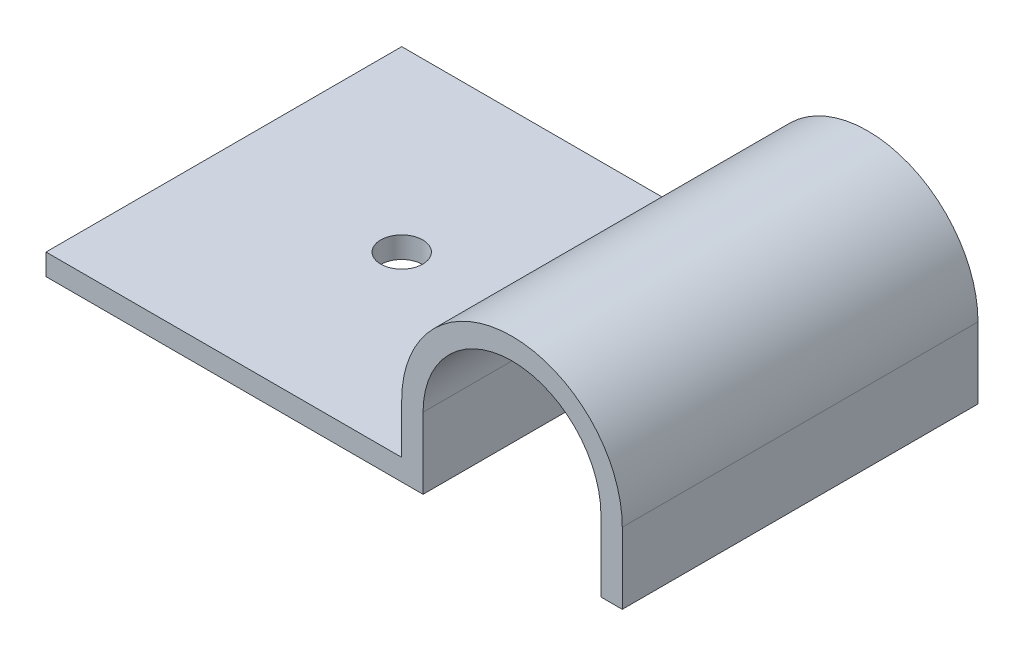
SolidWorks part; units mm, degrees
ref_plane "Front Plane" through (0, 0, 0) normal (0, 0, 1) x (1, 0, 0)
ref_plane "Top Plane" through (0, 0, 0) normal (0, 1, 0) x (1, 0, 0)
ref_plane "Right Plane" through (0, 0, 0) normal (1, 0, 0) x (0, 0, -1)
ref_plane "Plane1" through (0, 0, 0) normal (0, 0, -1) x (-1, 0, 0)
sketch "Sketch1" plane through (0, 0, 0) normal (0, 0, -1) x (-1, 0, 0)
  line L0 (7.9375, 2.8575) -> (9.4615, 2.8575)
  line L1 (9.4615, 2.8575) -> (9.4615, 7.9375)
  line L3 (7.9375, 7.9375) -> (7.9375, 2.8575)
  line L6 (-6.2865, 7.9375) -> (-6.2865, 2.8575)
  line L7 (-6.2865, 2.8575) -> (-4.7625, 2.8575)
  line L8 (-4.7625, 7.9375) -> (-4.7625, 2.8575)
  arc A0 (9.4615, 7.9375) -> (-6.2865, 7.9375) centre (1.5875, 7.9375) ccw
  arc A1 (-4.7625, 7.9375) -> (7.9375, 7.9375) centre (1.5875, 7.9375) cw
  dimension "D1" = 6.35
  dimension "D2" = 5.08
extrude "Boss-Extrude1" add sketch "Sketch1" against normal blind 25.4
sketch "Sketch2" plane through (-9.4615, 0, 0) normal (-1, 0, 0) x (0, 0, 1)
  line L0 (25.4, 4.3815) -> (25.4, 2.8575)
  line L1 (25.4, 2.8575) -> (0, 2.8575)
  line L2 (0, 2.8575) -> (0, 4.3815)
  line L3 (0, 4.3815) -> (25.4, 4.3815)
  line L5 (25.4, 2.8575) -> (0, 2.8575) construction
  dimension "D1" = 25.4
extrude "Boss-Extrude2" add sketch "Sketch2" along normal blind 25.4
sketch "Sketch5" plane through (0, 4.3815, 0) normal (0, 1, 0) x (1, 0, 0)
  line L0 (-9.4615, -25.4) -> (-9.4615, 0) construction
  line L1 (-34.8615, -25.4) -> (-9.4615, -25.4) construction
  circle A0 centre (-22.1615, -12.7) radius 1.5
  dimension "D1" = 12.7
  dimension "D2" = 12.7
  dimension "D3" = 3
extrude "Cut-Extrude1" cut sketch "Sketch5" against normal blind 2.54
